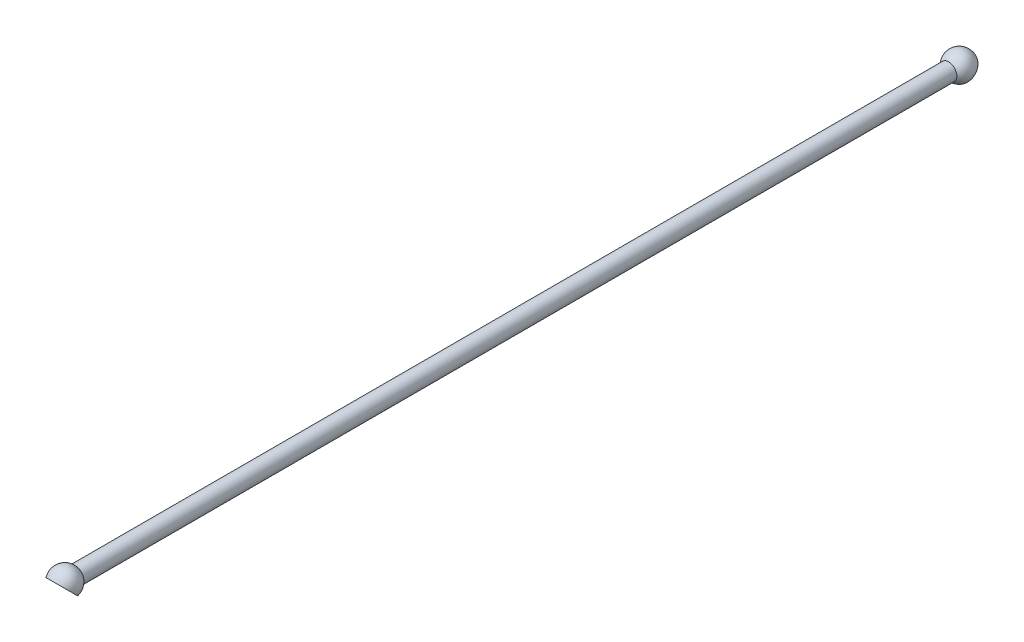
SolidWorks part; units mm, degrees
material "1060 Alloy"
ref_plane "Front Plane" through (0, 0, 0) normal (0, 0, 1) x (1, 0, 0)
ref_plane "Top Plane" through (0, 0, 0) normal (0, 1, 0) x (1, 0, 0)
ref_plane "Right Plane" through (0, 0, 0) normal (1, 0, 0) x (0, 0, -1)
sketch "Sketch1" plane through (0, 0, 0) normal (0, 0, 1) x (1, 0, 0)
  circle A0 centre (0, 0) radius 4
  dimension "D1" = 8
extrude "Boss-Extrude1" add sketch "Sketch1" along normal up to vertex (214.0808 mm away) and the other way up to vertex (214.0808 mm away)
ref_plane "Plane3" through (0, 0, 0) normal (0, 0, -1) x (-1, 0, 0)
ref_plane "Plane2" through (0, 0, 0) normal (0, 0, 1) x (1, 0, 0)
sketch "Sketch4" plane through (0, 0, 214.0808) normal (0, 0, 1) x (1, 0, 0)
  line L0 (-4, 0) -> (4, 0) construction
  circle A0 centre (0, 0) radius 4 construction
ref_plane "Plane1" through (0, 107.0404, 107.0404) normal (0, -0.7071, -0.7071) x (1, 0, 0)
sketch "Sketch3" plane through (0, 0, 0) normal (1, 0, 0) x (0, 0, -1)
  line L0 (-214.0808, 4) -> (-214.0808, -4) construction
  line L1 (-220.5808, 0) -> (-207.5808, 0)
  arc A1 (-207.5808, 0) -> (-220.5808, 0) centre (-214.0808, 0) ccw
  dimension "D1" = 6.5
revolve "Revolve1" add sketch "Sketch3" angle 360 about L1
sketch "Sketch5" plane through (0, 107.0404, 107.0404) normal (0, -0.7071, -0.7071) x (1, 0, 0)
  line L0 (-4, 151.378) -> (4, 151.378) construction
  line L1 (-10, 158.378) -> (10, 158.378)
  line L2 (-10, 158.378) -> (-10, 153.378)
  line L3 (-10, 153.378) -> (10, 153.378)
  line L4 (10, 158.378) -> (10, 153.378)
  point P6 (0, 153.378)
  point P7 (0, 151.378)
  dimension "D1" = 20
  dimension "D2" = 5
  dimension "D3" = 2
extrude "Cut-Extrude1" cut sketch "Sketch5" against normal through all both and the other way through all
sketch "Sketch6" plane through (0, 0, 0) normal (0, 1, 0) x (1, 0, 0)
  line L0 (-4, -214.0808) -> (4, -214.0808) construction
  line L1 (0, -209.0808) -> (0, -219.0808)
  arc A0 (0, -219.0808) -> (0, -209.0808) centre (0, -214.0808) ccw
  dimension "D1" = 10
revolve "Cut-Revolve1" cut sketch "Sketch6" angle 360 about L1
mirror "Mirror2" about plane through (0, 0, 0) normal (0, 0, 1) of "Cut-Revolve1", "Cut-Extrude1", "Revolve1"
